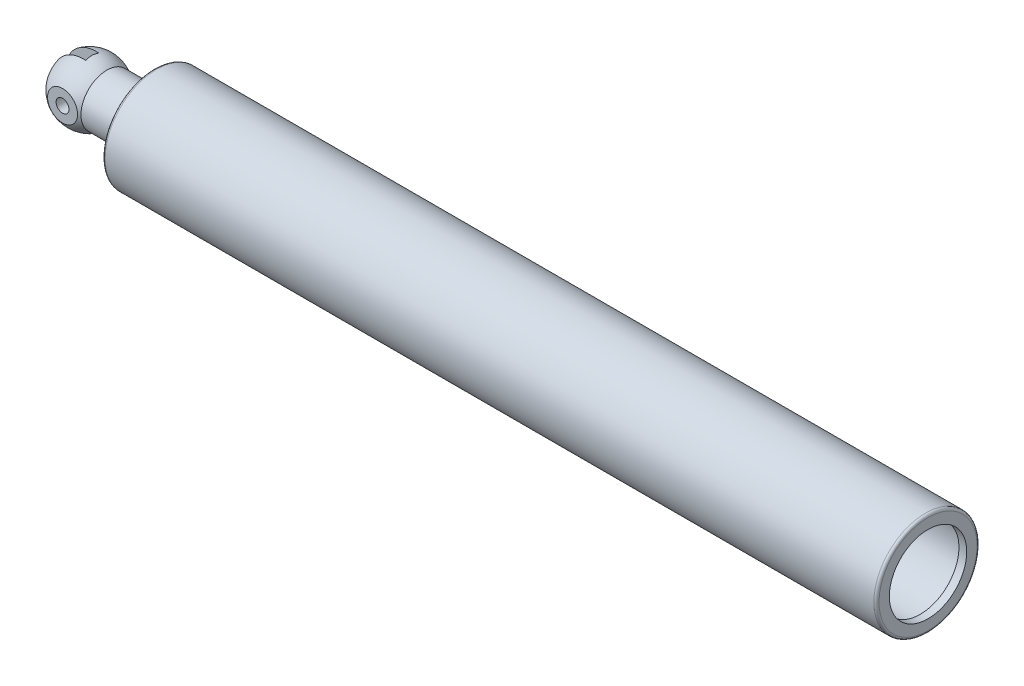
SolidWorks part; units mm, degrees
ref_plane "Front Plane" through (0, 0, 0) normal (0, 0, 1) x (1, 0, 0)
ref_plane "Top Plane" through (0, 0, 0) normal (0, 1, 0) x (1, 0, 0)
ref_plane "Right Plane" through (0, 0, 0) normal (1, 0, 0) x (0, 0, -1)
sketch "Sketch1" plane through (0, 0, 0) normal (0, 0, 1) x (1, 0, 0)
  line L0 (297, 15) -> (300, 15)
  line L1 (0, 0) -> (3, 0)
  line L2 (0, 10) -> (0, 20)
  line L3 (0, 20) -> (300, 20)
  line L4 (300, 15) -> (300, 20)
  line L6 (3, 0) -> (3, 17)
  line L7 (3, 17) -> (297, 17)
  line L8 (297, 15) -> (297, 17)
  line L12 (0, 10) -> (-18.3668, 10)
  line L13 (-37, 0) -> (0, 0)
  arc A0 (-18.3668, 10) -> (-37, 0) centre (-25, 0) ccw
  dimension "D10" = 12
  dimension "D11" = 25
  dimension "D1" = 300
  dimension "D2" = 20
  dimension "D3" = 3
  dimension "D4" = 3
  dimension "D5" = 3
  dimension "D6" = 15
  dimension "D7" = 10
revolve "Revolve1" add sketch "Sketch1" angle 360 about L1
sketch "Sketch4" plane through (0, 0, 0) normal (0, 1, 0) x (1, 0, 0)
  line L0 (-19.5, 2.5) -> (-19.5, -2.5)
  line L1 (-19.5, 2.5) -> (-37, 2.5)
  line L3 (-19.5, -2.5) -> (-37, -2.5)
  line L4 (-37, 2.5) -> (-37, -2.5)
  arc A0 (-18.3668, 10) -> (-18.3668, -10) centre (-25, 0) ccw construction
  point P9 (-37, 0)
  dimension "D1" = 5
  dimension "D2" = 17.5
sketch "Sketch6" plane through (0, 0, 0) normal (-1, 0, 0) x (0, 0, 1)
  line L1 (-10.5, 15) -> (10.5, 15)
  line L2 (-10.5, 15) -> (-10.5, -15)
  line L3 (-10.5, -15) -> (10.5, -15)
  line L4 (10.5, 15) -> (10.5, -15)
  line L5 (0, 15) -> (0, -15) construction
  point P4 (0, 15)
  point P11 (0, 0)
  dimension "D1" = 10.5
  dimension "D2" = 30
extrude "Cut-Extrude3" cut sketch "Sketch6" along normal blind 40 flip side to cut
revolve "Cut-Revolve1" cut sketch "Sketch4" angle 360 about L4
fillet "Fillet1" radius 1 3 edges at (0, 0, 10) (300, 0, 20) (0, 0, 20)
sketch "Sketch7" plane through (0, 0, 0) normal (0, 0, 1) x (1, 0, 0)
  line L0 (3, 0) -> (277, 0) construction
  line L3 (297, 15) -> (297, 17) construction
  point P4 (0, 0)
  point P7 (193.3222, 0)
  dimension "D1" = 20
sketch "Sketch8" plane through (0, 0, 10.5) normal (0, 0, 1) x (1, 0, 0)
  circle A0 centre (-25, 0) radius 2.5
  dimension "D1" = 5
extrude "Cut-Extrude4" cut sketch "Sketch8" against normal through all both and the other way through all
